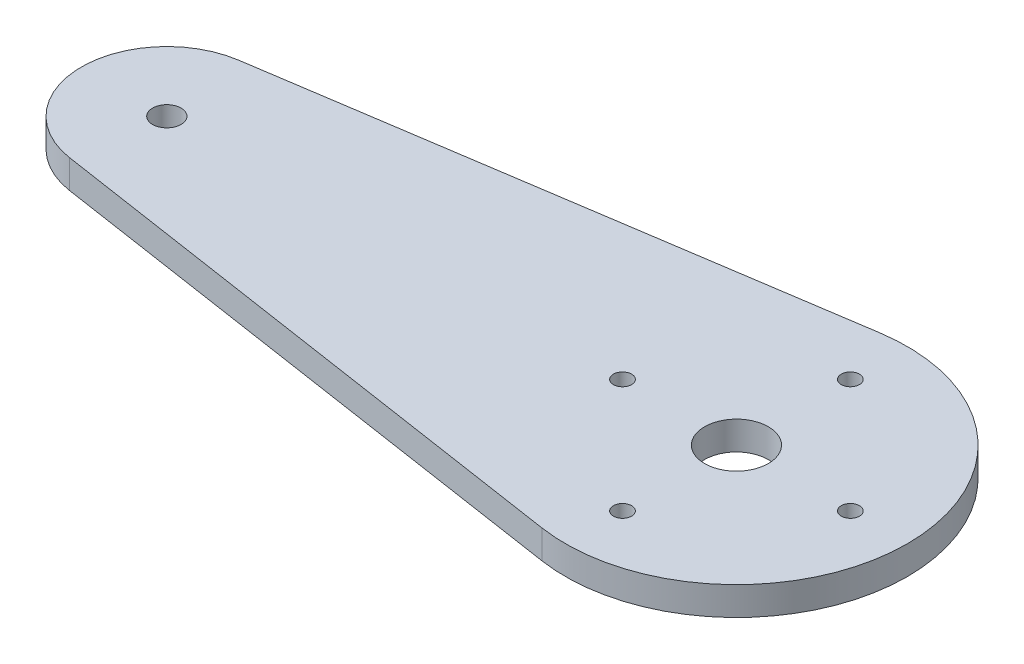
SolidWorks part; units mm, degrees
ref_plane "Front Plane" through (0, 0, 0) normal (0, 0, 1) x (1, 0, 0)
ref_plane "Top Plane" through (0, 0, 0) normal (0, 1, 0) x (1, 0, 0)
ref_plane "Right Plane" through (0, 0, 0) normal (1, 0, 0) x (0, 0, -1)
sketch "Sketch1" plane through (0, 0, 0) normal (0, 1, 0) x (1, 0, 0)
  line L0 (-64.9288, 9.4172) -> (-2.8575, 18.8345)
  line L1 (-64.9288, -9.4172) -> (-2.8575, -18.8345)
  line L2 (-111.3601, 0) -> (-50111.3601, 0) construction
  line L3 (0, -984.3615) -> (0, 49015.6385) construction
  line L4 (0, 0) -> (0, 12.7) construction
  line L5 (0, 0) -> (12.7, 0) construction
  arc A0 (-2.8575, -18.8345) -> (-2.8575, 18.8345) centre (0, 0) ccw
  arc A1 (-64.9288, 9.4172) -> (-64.9288, -9.4172) centre (-63.5, 0) ccw
  circle A2 centre (-63.5, 0) radius 1.5875
  circle A3 centre (0, 0) radius 3.556
  circle A4 centre (0, 12.7) radius 1.016
  circle A5 centre (12.7, 0) radius 1.016
  circle A6 centre (0, -12.7) radius 1.016
  circle A7 centre (-12.7, 0) radius 1.016
  dimension "D1" = 9.525
  dimension "D2" = 19.05
  dimension "D4" = 3.175
  dimension "D5" = 7.112
  dimension "D6" = 2.032
  dimension "D3" = 63.5
  dimension "D7" = 12.7
  dimension "D9" = 90
  dimension "D10" = 12.7
  dimension "D8" = 4
extrude "Boss-Extrude1" add sketch "Sketch1" along normal blind 3.175
